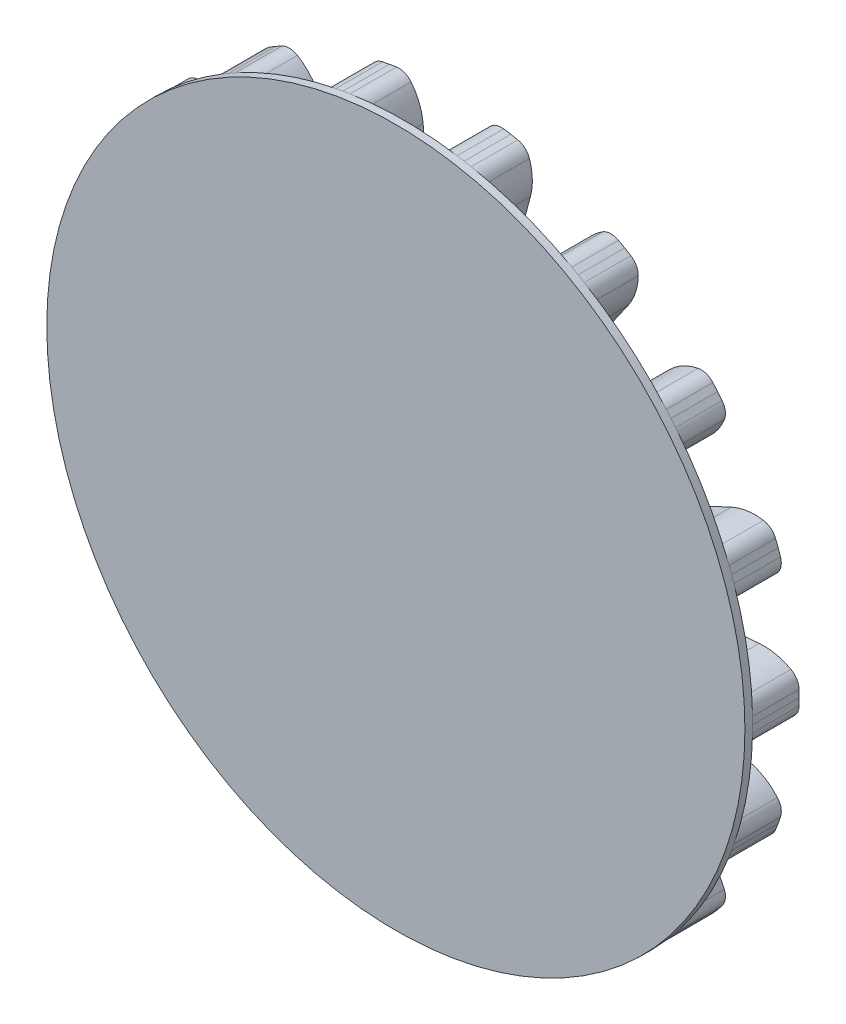
SolidWorks part; units mm, degrees
ref_plane "Plan de face" through (0, 0, 0) normal (0, 0, 1) x (1, 0, 0)
ref_plane "Plan de dessus" through (0, 0, 0) normal (0, 1, 0) x (1, 0, 0)
ref_plane "Plan de droite" through (0, 0, 0) normal (1, 0, 0) x (0, 0, -1)
sketch "Esquisse4" plane through (0, 0, 0) normal (0, 0, 1) x (1, 0, 0)
  line L0 (0, 0) -> (15.5601, 0) construction
  line L1 (0, 0) -> (17.2426, 1.5085) construction
  line L2 (0, 0) -> (17.0187, 3.0009) construction
  line L3 (0, 0) -> (17.2619, 0.7537) construction
  line L4 (17.4334, 1.5252) -> (19.9239, 1.7431)
  line L5 (17.2341, 3.0388) -> (0, 0)
  line L6 (22.4786, 0.9814) -> (22.5, 0)
  line L7 (22.4786, -0.9814) -> (22.5, 0)
  line L8 (17.4334, -1.5252) -> (19.9239, -1.7431)
  line L9 (17.2341, -3.0388) -> (0, 0)
  circle A0 centre (0, 0) radius 17.5 construction
  circle A1 centre (0, 0) radius 20 construction
  circle A2 centre (0, 0) radius 22.5 construction
  arc A3 (22.4786, 0.9814) -> (19.9239, 1.7431) centre (20.2394, -1.8636) ccw
  arc A4 (17.4334, 1.5252) -> (17.2341, 3.0388) centre (0, 0) ccw
  arc A5 (22.4786, -0.9814) -> (19.9239, -1.7431) centre (20.2394, 1.8636) cw
  arc A6 (17.4334, -1.5252) -> (17.2341, -3.0388) centre (0, 0) cw
  dimension "D1" = 45
  dimension "D2" = 40
  dimension "D3" = 35
  dimension "D4" = 10
  dimension "D5" = 5
  dimension "D6" = 2.5
extrude "Boss.-Extru.4" add sketch "Esquisse4" along normal blind 3 contours A6 L8 A5 L7 L6 A3 L4 A4 L5 L9
fillet "Congé1" radius 0.7 2 edges at (17.4334, 1.5252, 1.5) (17.4334, -1.5252, 1.5)
fillet "Congé2" radius 1 2 edges at (22.4786, 0.9814, 1.5) (22.4786, -0.9814, 1.5)
pattern_circular "Répétition circulaire1" count 18 over 360 about axis through (0, 0, 0) along (0, 0, 1) of bodies 103
sketch "Esquisse5" plane through (0, 0, 3) normal (0, 0, 1) x (1, 0, 0)
  circle A0 centre (0, 0) radius 2.5
  dimension "D1" = 5
extrude "Enlèv. mat.-Extru.1" cut sketch "Esquisse5" against normal through all
sketch "Esquisse6" plane through (0, 0, 3) normal (0, 0, 1) x (1, 0, 0)
  line L0 (2.3266, -14.6966) -> (3.4593, -2.2875)
  line L1 (-2.1506, 14.6966) -> (-3.4593, 2.2875)
  line L2 (2.1506, 14.6966) -> (-2.1506, 14.6966) construction
  line L3 (-2.1506, 14.6966) -> (-2.1506, -14.6966) construction
  spline S0 degree 3 poles (3.4593, -2.2875) (3.5096, -1.6181) (3.6101, -0.2794) (3.1935, 5.4003) (2.6347, 10.3813) (2.1506, 14.6966) knots 0 0 0 0 0.117897 0.235794 1 1 1 1
  spline S1 degree 3 poles (2.1506, 14.6966) (2.0958, 14.9572) (1.986, 15.4784) (1.4792, 16.1192) (0.7953, 16.5428) (0, 16.6903) (-0.7953, 16.5428) (-1.4792, 16.1192) (-1.986, 15.4784) (-2.0958, 14.9572) (-2.1506, 14.6966) knots 0 0 0 0 0.124995 0.250006 0.375 0.5 0.625 0.749994 0.875005 1 1 1 1
  spline S2 degree 3 poles (-2.1506, -14.6966) (-2.0935, -14.9679) (-1.9793, -15.5104) (-1.4518, -16.1774) (-0.7398, -16.6183) (0.088, -16.7719) (0.9158, -16.6183) (1.6278, -16.1774) (2.1553, -15.5104) (2.2695, -14.9679) (2.3266, -14.6966) knots 0 0 0 0 0.124995 0.250006 0.375 0.5 0.625 0.749994 0.875005 1 1 1 1
  spline S3 degree 3 poles (-3.4593, 2.2875) (-3.5096, 1.6181) (-3.6101, 0.2794) (-3.1935, -5.4003) (-2.6347, -10.3813) (-2.1506, -14.6966) knots 0 0 0 0 0.117897 0.235794 1 1 1 1
  point P9 (-2.1506, 0)
  point P10 (0, 14.6966)
extrude "Enlèv. mat.-Extru.2" cut sketch "Esquisse6" against normal through all
sketch "Esquisse7" plane through (0, 0, 3) normal (0, 0, 1) x (1, 0, 0)
  circle A0 centre (0, 0) radius 4.0185
extrude "Enlèv. mat.-Extru.3" cut sketch "Esquisse7" against normal blind 10
sketch "Esquisse8" plane through (0, 0, 3) normal (0, 0, 1) x (1, 0, 0)
  circle A0 centre (0, 0) radius 22.5
extrude "Boss.-Extru.5" add sketch "Esquisse8" along normal blind 0.5
